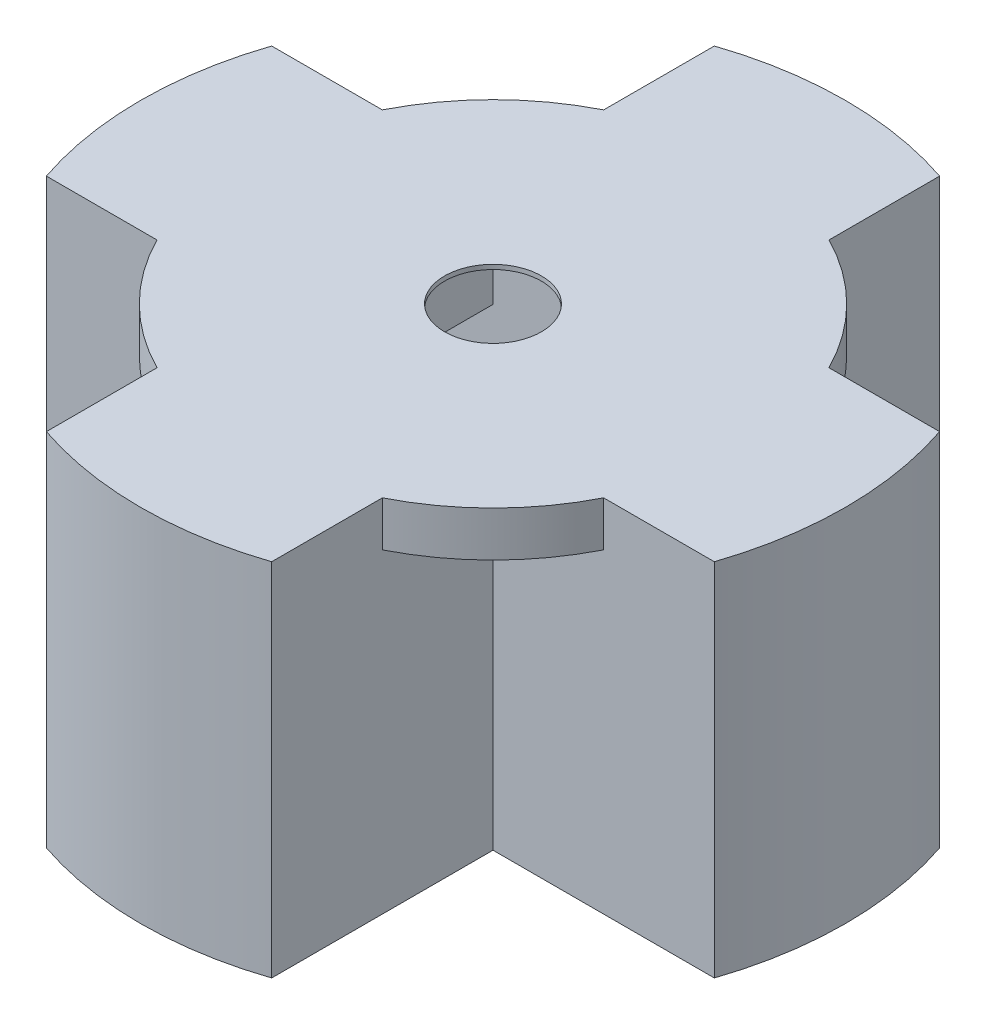
SolidWorks part; units mm, degrees
ref_plane "Front Plane" through (0, 0, 0) normal (0, 0, 1) x (1, 0, 0)
ref_plane "Top Plane" through (0, 0, 0) normal (0, 1, 0) x (1, 0, 0)
ref_plane "Right Plane" through (0, 0, 0) normal (1, 0, 0) x (0, 0, -1)
sketch "Sketch1" plane through (0, 0, 0) normal (0, 1, 0) x (1, 0, 0)
  line L0 (0, 0) -> (-40.2717, 0)
  line L1 (-40.2717, 0) -> (-40.2717, -19.7104)
  line L2 (-40.2717, -19.7104) -> (0, -19.7104)
  line L3 (0, -19.7104) -> (0, 0)
  line L4 (-47.5043, 2.8448) -> (7.2327, 2.8448)
  line L13 (-47.5043, 2.8448) -> (-47.5043, -22.5552)
  line L14 (-47.5043, -22.5552) -> (7.2327, -22.5552)
  line L15 (7.2327, -22.5552) -> (7.2327, 2.8448)
  circle A0 centre (-30.4165, -9.8552) radius 9.8552
  circle A1 centre (-30.4165, -9.8552) radius 6.5659
  circle A2 centre (-30.4165, -9.8552) radius 5.3594
  point P13 (7.5651, 3.0281)
  dimension "D3" = 13.1318
  dimension "D4" = 10.7188
  dimension "D1" = 40.2717
  dimension "D2" = 19.7104
  dimension "D5" = 54.737
  dimension "D6" = 25.4
  dimension "D7" = 7.2326
  dimension "D8" = 2.8448
extrude "Boss-Extrude2" add sketch "Sketch1" along normal blind 9.906 contours L14 L15 L4 L13 L3 L2 L1 L0
sketch "Sketch3" plane through (0, 9.906, 0) normal (0, 1, 0) x (1, 0, 0)
  line L2 (-40.2717, 0) -> (0, 0)
  line L3 (-40.2717, 0) -> (-40.2717, -19.7104)
  line L4 (-40.2717, -19.7104) -> (0, -19.7104)
  line L5 (0, 0) -> (0, -19.7104)
  circle A1 centre (-30.4165, -9.8552) radius 9.8552
  circle A2 centre (-30.4165, -9.8552) radius 5.461
  line M8 (0, 0) -> (0, -19.7104)
  line M9 (0, -19.7104) -> (-40.2717, -19.7104)
  line M10 (-40.2717, -19.7104) -> (-40.2717, 0)
  line M11 (-40.2717, 0) -> (0, 0)
  dimension "D1" = 19.7104
  dimension "D3" = 10.922
  dimension "D2" = 9.8552
extrude "Boss-Extrude3" add sketch "Sketch3" against normal blind 0.508 contours A1 A2 | A1 L4 M10 | A1 L2 M9 M8 | A1 L3 M11
sketch "Sketch9" plane through (0, 0, 0) normal (0, -1, 0) x (1, 0, 0)
  line L0 (-47.5043, 9.2202) -> (-47.5043, 10.4902)
  line L1 (-47.5043, -2.8448) -> (-47.5043, 22.5552) construction
  line L2 (-47.5043, 10.4902) -> (-40.2717, 10.4902)
  line L3 (-40.2717, 19.7104) -> (-40.2717, 0) construction
  line L4 (-40.2717, 10.4902) -> (-40.2717, 9.2202)
  line L5 (-40.2717, 0) -> (-40.2717, 19.7104) construction
  line L6 (-40.2717, 9.2202) -> (-47.5043, 9.2202)
  line L7 (-20.1358, 22.5552) -> (-20.1358, -2.8448) construction
  line L8 (-47.5043, 22.5552) -> (7.2327, 22.5552) construction
  line L9 (-47.5043, -2.8448) -> (7.2327, -2.8448) construction
  line L10 (0, 10.4902) -> (0, 9.2202)
  line L11 (7.2327, 10.4902) -> (0, 10.4902)
  line L12 (7.2327, 9.2202) -> (7.2327, 10.4902)
  line L13 (0, 9.2202) -> (7.2327, 9.2202)
  point P5 (-47.5043, 9.8552)
  point P8 (-47.5043, 9.8552)
  dimension "D1" = 1.27
extrude "Cut-Extrude2" cut sketch "Sketch9" against normal blind 5.08 contours L6 L0 L2 L4 | L10 L13 L12 L11
sketch "Sketch12" plane through (0, 0, 0) normal (0, -1, 0) x (1, 0, 0)
  line L0 (-47.5043, 22.5552) -> (7.2327, 22.5552) construction
  line L1 (-47.5043, 19.7104) -> (7.2327, 19.7104)
  line L2 (-47.5043, 19.7104) -> (-47.5043, 22.5552)
  line L3 (-47.5043, 22.5552) -> (7.2327, 22.5552)
  line L4 (7.2327, 19.7104) -> (7.2327, 22.5552)
  line L5 (-40.2717, 19.7104) -> (0, 19.7104) construction
  line L6 (-47.5043, 9.8552) -> (7.2327, 9.8552) construction
  line L7 (-47.5043, 9.2202) -> (-47.5043, 10.4902) construction
  line L8 (7.2327, 9.2202) -> (7.2327, 10.4902) construction
  line L9 (-47.5043, -2.8448) -> (7.2327, -2.8448)
  line L10 (7.2327, 0) -> (7.2327, -2.8448)
  line L11 (-47.5043, 0) -> (7.2327, 0)
  line L12 (-47.5043, 0) -> (-47.5043, -2.8448)
  line L13 (-47.5043, 10.4902) -> (-47.5043, 22.5552) construction
  line L14 (7.2327, 22.5552) -> (7.2327, 10.4902) construction
extrude "Boss-Extrude4" add sketch "Sketch12" along normal blind 30.734
sketch "Sketch17" plane through (0, 9.906, 0) normal (0, 1, 0) x (1, 0, 0)
  line L0 (-35.8775, -9.8552) -> (-24.9555, -9.8552) construction
  line L1 (-30.4165, -4.3942) -> (-30.4165, -15.3162) construction
  line L2 (-24.9555, -9.8552) -> (7.2327, -9.8552)
  line L3 (7.2327, -22.5552) -> (7.2327, 2.8448) construction
  line L4 (-30.4165, -15.3162) -> (-30.4165, -47.5044)
  line L5 (-35.8775, -9.8552) -> (-68.0656, -9.8552)
  line L6 (-30.4165, -4.3942) -> (-30.4165, 27.7939)
  line L7 (-47.5043, 2.8448) -> (-68.0656, 2.8448)
  line L8 (-47.5043, -22.5552) -> (-68.0656, -22.5552)
  line L9 (-68.0656, -22.5552) -> (-68.0656, 2.8448)
  line L10 (-17.7165, 27.7939) -> (-43.1165, 27.7939)
  line L11 (-43.1165, 27.7939) -> (-43.1165, 2.8448)
  line L12 (-47.5043, 2.8448) -> (7.2327, 2.8448) construction
  line L13 (-17.7165, 27.7939) -> (-17.7165, 2.8448)
  line L14 (-17.7165, -47.5044) -> (-43.1165, -47.5044)
  line L15 (-43.1165, -47.5044) -> (-43.1165, -22.5552)
  line L16 (-47.5043, -22.5552) -> (7.2327, -22.5552) construction
  line L17 (-17.7165, -47.5044) -> (-17.7165, -22.5552)
  line L18 (-17.7165, -22.5552) -> (-43.1165, -22.5552)
  line L19 (-17.7165, 2.8448) -> (-43.1165, 2.8448)
  line L20 (-47.5043, -22.5552) -> (-47.5043, 2.8448)
  circle A0 centre (-30.4165, -9.8552) radius 5.461 construction
  point P19 (-30.4165, -9.8552)
  point P23 (-30.4165, 27.7939)
  point P30 (-30.4165, -47.5044)
  dimension "D2" = 25.4
  dimension "D3" = 25.4
  dimension "D1" = 4
sketch "Sketch19" plane through (-47.5043, 0, 0) normal (-1, 0, 0) x (0, 0, 1)
  line L0 (-2.8448, -30.734) -> (0, -30.734)
  line L1 (0, -30.734) -> (0, 0)
  line L2 (0, 0) -> (19.7104, 0)
  line L3 (19.7104, 0) -> (19.7104, -30.734)
  line L4 (19.7104, -30.734) -> (22.5552, -30.734)
  line L5 (22.5552, -30.734) -> (22.5552, 9.906)
  line L6 (22.5552, 9.906) -> (-2.8448, 9.906)
  line L7 (-2.8448, 9.906) -> (-2.8448, -30.734)
extrude "Boss-Extrude5" add sketch "Sketch19" along normal up to vertex (20.5613 mm away) up to point (-68.0656, 9.906, 9.8552)
sketch "Sketch20" plane through (0, 0, -2.8448) normal (0, 0, -1) x (-1, 0, 0)
  line L0 (17.7165, 9.906) -> (43.1165, 9.906)
  line L1 (43.1165, 9.906) -> (43.1165, -30.734)
  line L2 (68.0656, -30.734) -> (-7.2327, -30.734) construction
  line L4 (17.7165, -30.734) -> (17.7165, 9.906)
  line L5 (43.1165, -30.734) -> (40.3225, -30.734)
  line L6 (40.3225, -30.734) -> (40.3225, 0)
  line L7 (40.3225, 0) -> (20.5105, 0)
  line L8 (20.5105, 0) -> (20.5105, -30.734)
  line L9 (20.5105, -30.734) -> (17.7165, -30.734)
  dimension "D1" = 2.794
  dimension "D2" = 2.794
  dimension "D3" = 9.906
extrude "Boss-Extrude6" add sketch "Sketch20" along normal up to vertex (24.9491 mm away) up to point (-17.7165, 9.906, -27.7939)
sketch "Sketch21" plane through (0, 0, 22.5552) normal (0, 0, 1) x (1, 0, 0)
  line L0 (-43.1165, 9.906) -> (-43.1165, -30.734)
  line L1 (7.2327, -30.734) -> (-68.0657, -30.734) construction
  line L2 (-43.1165, 9.906) -> (-17.7165, 9.906)
  line L3 (-17.7165, 9.906) -> (-17.7165, -30.734)
  line L4 (-43.1165, -30.734) -> (-40.3225, -30.734)
  line L5 (-40.3225, -30.734) -> (-40.3225, 0)
  line L6 (-40.3225, 0) -> (-20.5105, 0)
  line L7 (-20.5105, 0) -> (-20.5105, -30.734)
  line L8 (-20.5105, -30.734) -> (-17.7165, -30.734)
  dimension "D1" = 2.794
  dimension "D2" = 2.794
  dimension "D3" = 9.906
extrude "Boss-Extrude7" add sketch "Sketch21" along normal up to vertex (24.9491 mm away) up to point (-43.1165, 9.906, 47.5044)
sketch "Sketch23" plane through (0, 9.906, 0) normal (0, 1, 0) x (1, 0, 0)
  line L0 (-35.8775, -9.8552) -> (-24.9555, -9.8552) construction
  line L1 (-17.7165, 27.7939) -> (-43.1165, 27.7939) construction
  line L2 (-17.7165, -22.5552) -> (7.2327, -22.5552) construction
  line L3 (-17.7165, -47.5044) -> (-43.1165, -47.5044) construction
  line L4 (-47.5043, 2.8448) -> (-68.0656, 2.8448) construction
  line L5 (-68.0656, 2.8448) -> (-68.0656, -22.5552)
  line L6 (-43.1165, -47.5044) -> (-17.7165, -47.5044)
  line L7 (7.2327, -22.5552) -> (7.2327, 2.8448)
  line L8 (-17.7165, 27.7939) -> (-43.1165, 27.7939)
  arc A0 (-43.1165, 27.7939) -> (-17.7165, 27.7939) centre (-30.4165, -9.8552) cw
  arc A1 (7.2327, 2.8448) -> (7.2327, -22.5552) centre (-30.4165, -9.8552) cw
  arc A2 (-17.7165, -47.5044) -> (-43.1165, -47.5044) centre (-30.4165, -9.8552) cw
  arc A3 (-68.0656, -22.5552) -> (-68.0656, 2.8448) centre (-30.4165, -9.8552) cw
extrude "Boss-Extrude8" add sketch "Sketch23" against normal up to vertex (40.64 mm away)
sketch "Sketch24" plane through (0, 9.906, 0) normal (0, 1, 0) x (1, 0, 0)
  line L9 (-68.0656, 2.8448) -> (-43.1165, 2.8448)
  line L10 (-43.1165, 27.7939) -> (-43.1165, 2.8448) construction
  line L11 (-17.7165, 27.7939) -> (-17.7165, 2.8448) construction
  line L12 (-17.7165, 2.8448) -> (7.2327, 2.8448) construction
  line L13 (-17.7165, -22.5552) -> (7.2327, -22.5552) construction
  line L14 (-17.7165, -47.5044) -> (-17.7165, -22.5552) construction
  line L15 (-43.1165, -47.5044) -> (-43.1165, -22.5552) construction
  line L16 (-47.5043, -22.5552) -> (-68.0656, -22.5552) construction
  line L17 (-55.5911, 2.8448) -> (-43.1165, 2.8448)
  line L18 (-43.1165, 15.3194) -> (-43.1165, 2.8448)
  line L19 (-17.7165, 15.3194) -> (-17.7165, 2.8448)
  line L20 (-17.7165, 2.8448) -> (-5.2419, 2.8448)
  line L21 (-5.2419, -22.5552) -> (-17.7165, -22.5552)
  line L22 (-17.7165, -22.5552) -> (-17.7165, -35.0298)
  line L23 (-43.1165, -35.0298) -> (-43.1165, -22.5552)
  line L24 (-43.1165, -22.5552) -> (-55.5911, -22.5552)
  arc A0 (-55.5911, 2.8448) -> (-43.1165, 15.3194) centre (-30.4165, -9.8552) cw
  arc A1 (-17.7165, 15.3194) -> (-5.2419, 2.8448) centre (-30.4165, -9.8552) cw
  arc A2 (-5.2419, -22.5552) -> (-17.7165, -35.0298) centre (-30.4165, -9.8552) cw
  arc A3 (-43.1165, -35.0298) -> (-55.5911, -22.5552) centre (-30.4165, -9.8552) cw
  line M2 (-68.0657, -22.5552) -> (-43.1165, -22.5552)
  line M3 (-43.1165, -22.5552) -> (-43.1165, -47.5044)
  line M5 (-17.7165, -47.5044) -> (-17.7165, -22.5552)
  line M6 (-17.7165, -22.5552) -> (7.2327, -22.5552)
  line M8 (7.2327, 2.8448) -> (-17.7165, 2.8448)
  line M9 (-17.7165, 2.8448) -> (-17.7165, 27.7939)
  line M11 (-43.1165, 27.7939) -> (-43.1165, 2.8448)
  line M12 (-43.1165, 2.8448) -> (-68.0656, 2.8448)
extrude "Boss-Extrude9" add sketch "Sketch24" against normal blind 5.08 contours A0 M12 M11 | A3 M3 M2 | A2 M6 M5 | A1 M9 M8
sketch "Sketch25" plane through (0, -30.734, 0) normal (0, -1, 0) x (1, 0, 0)
  line L0 (-68.0656, 6.6802) -> (-68.0656, 13.0302)
  line L1 (-68.0656, 22.5552) -> (-68.0656, -2.8448) construction
  line L2 (-68.0656, 13.0302) -> (-70.6056, 13.0302)
  line L3 (-70.6056, 13.0302) -> (-70.6056, 6.6802)
  line L4 (-70.6056, 6.6802) -> (-68.0656, 6.6802)
  point P6 (-68.0656, 9.8552)
  dimension "D1" = 6.35
  dimension "D2" = 2.54
extrude "Cut-Extrude3" cut sketch "Sketch25" against normal blind 2.54
